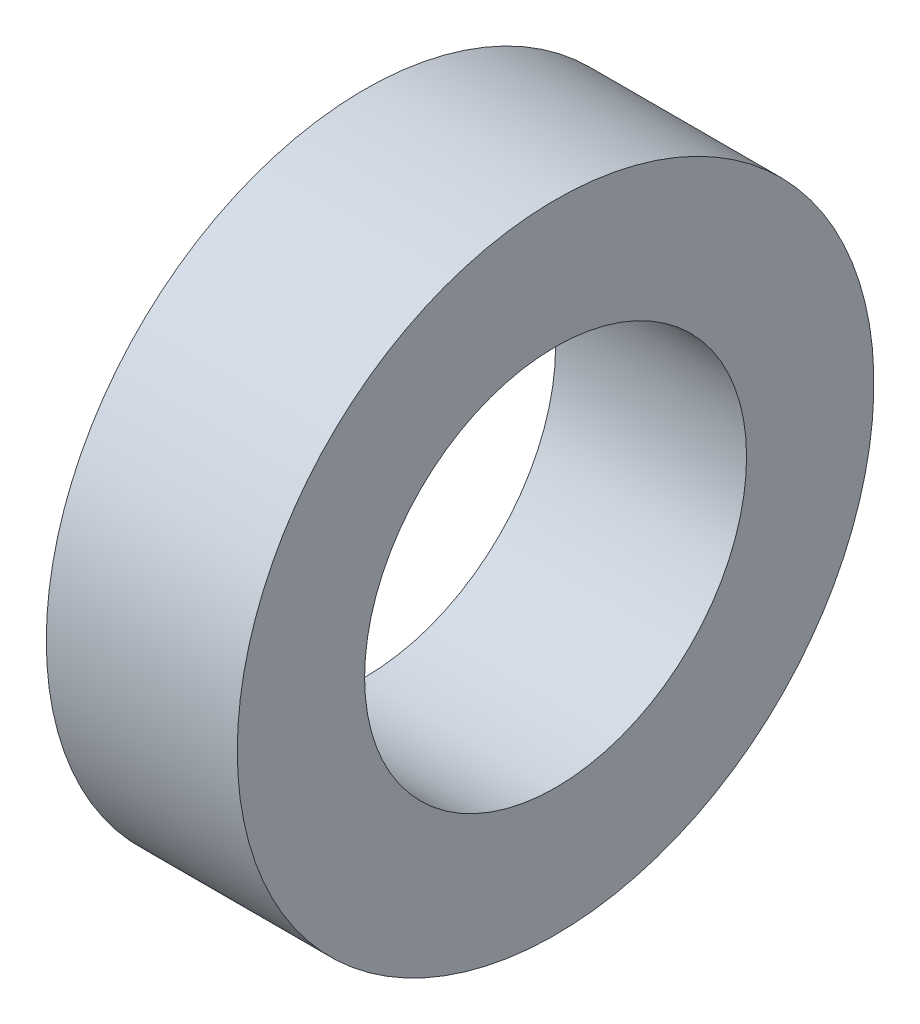
SolidWorks part; units mm, degrees
ref_plane "Front Plane" through (0, 0, 0) normal (0, 0, 1) x (1, 0, 0)
ref_plane "Top Plane" through (0, 0, 0) normal (0, 1, 0) x (1, 0, 0)
ref_plane "Right Plane" through (0, 0, 0) normal (1, 0, 0) x (0, 0, -1)
sketch "Sketch1" plane through (0, 0, 0) normal (0, 0, 1) x (1, 0, 0)
  line L0 (0, 0) -> (3, 0) construction
  line L1 (0, 3) -> (0, 5)
  line L4 (0, 5) -> (3, 5)
  line L5 (3, 5) -> (3, 3)
  line L6 (3, 3) -> (0, 3)
  dimension "D1" = 3
  dimension "D3" = 5
  dimension "D4" = 3
revolve "Revolve1" add sketch "Sketch1" angle 360 about L0
